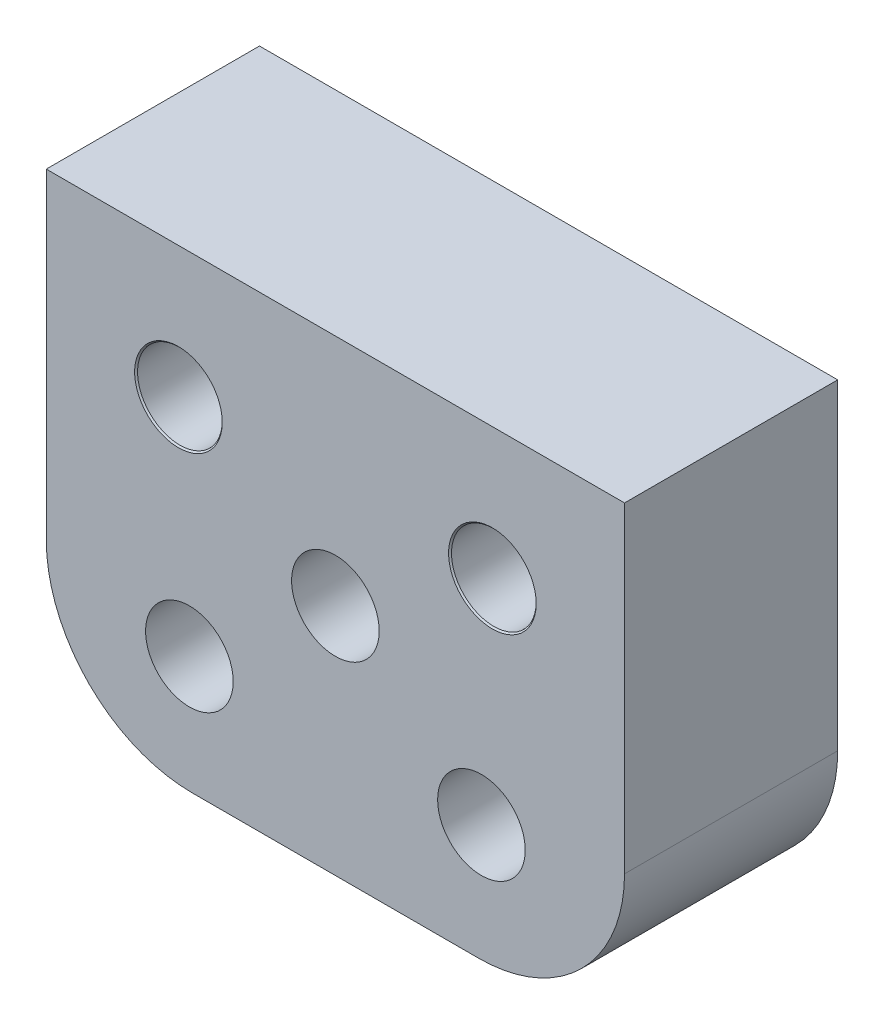
SolidWorks part; units mm, degrees
ref_plane "Спереди" through (0, 0, 0) normal (0, 0, 1) x (1, 0, 0)
ref_plane "Сверху" through (0, 0, 0) normal (0, 1, 0) x (1, 0, 0)
ref_plane "Справа" through (0, 0, 0) normal (1, 0, 0) x (0, 0, -1)
other "Configuration Table"
sketch "Эскиз1" plane through (0, 0, 0) normal (0, 0, 1) x (1, 0, 0)
  line L0 (9.9, 16) -> (9.9, -0.7731) construction
  line L1 (5, 0) -> (14.8, 0)
  line L2 (0, 5) -> (0, 16)
  line L3 (0, 16) -> (19.8, 16)
  line L4 (19.8, 5) -> (19.8, 16)
  arc A0 (14.8, 0) -> (19.8, 5) centre (14.8, 5) ccw
  arc A1 (0, 5) -> (5, 0) centre (5, 5) ccw
  circle A3 centre (9.9, 8) radius 1.5
  circle A4 centre (4.525, 11.5) radius 1.25
  circle A5 centre (4.9, 4) radius 1.5
  circle A6 centre (14.9, 4) radius 1.5
  circle A7 centre (15.275, 11.5) radius 1.25
  point P7 (19.8, 0)
  point P10 (0, 0)
  dimension "D3" = 5
  dimension "D4" = 2.5
  dimension "D5" = 3
  dimension "D6" = 3
  dimension "D9" = 10
  dimension "D10" = 10.75
  dimension "D11" = 3.5
  dimension "D1" = 19.8
  dimension "D2" = 16
  dimension "D7" = 4.5
  dimension "D8" = 12
extrude "Бобышка-Вытянуть1" add sketch "Эскиз1" against normal blind 7.3
hole_wizard "Зенковка для  винта с плоской головкой M2.51" positions "Трехмерный эскиз1" profile "Эскиз2" countersink size "M2.5" standard "Ansi Metric" end condition through all
sketch3d "Трехмерный эскиз1"
  line L0 (4.525, 11.5, -7.3) -> (4.525, 11.5, 0) construction
  line L1 (15.275, 11.5, -7.3) -> (15.275, 11.5, 0) construction
  point P0 (4.525, 11.5, 0)
  point P4 (15.275, 11.5, 0)
sketch "Эскиз2" plane through (4.525, 11.5, 0) normal (1, 0, 0) x (0, -1, 0)
  line L0 (0, 0) -> (0, 7.3)
  line L1 (0, 7.3) -> (1.5, 7.3)
  line L2 (1.45, 7.25) -> (1.45, 0.05)
  line L3 (1.45, 0.05) -> (1.5, 0)
  line L5 (1.5, 0) -> (0, 0)
  line L6 (-1.45, 0.05) -> (-1.5, 0) construction
  line L7 (1.5, 7.3) -> (1.45, 7.25)
  line L8 (-1.5, 7.3) -> (-1.45, 7.25) construction
  line L11 (0, -6.35) -> (0, 107.95) construction
  dimension "Диаметр сквозного отверстия" = 2.9
  dimension "Глубина сквозного отверстия" = 7.3
  dimension "Диаметр передней зенковки" = 3
  dimension "Угол передней зенковки" = 90
  dimension "Диаметр задней зенковки" = 3
  dimension "Угол задней зенковки" = 90
